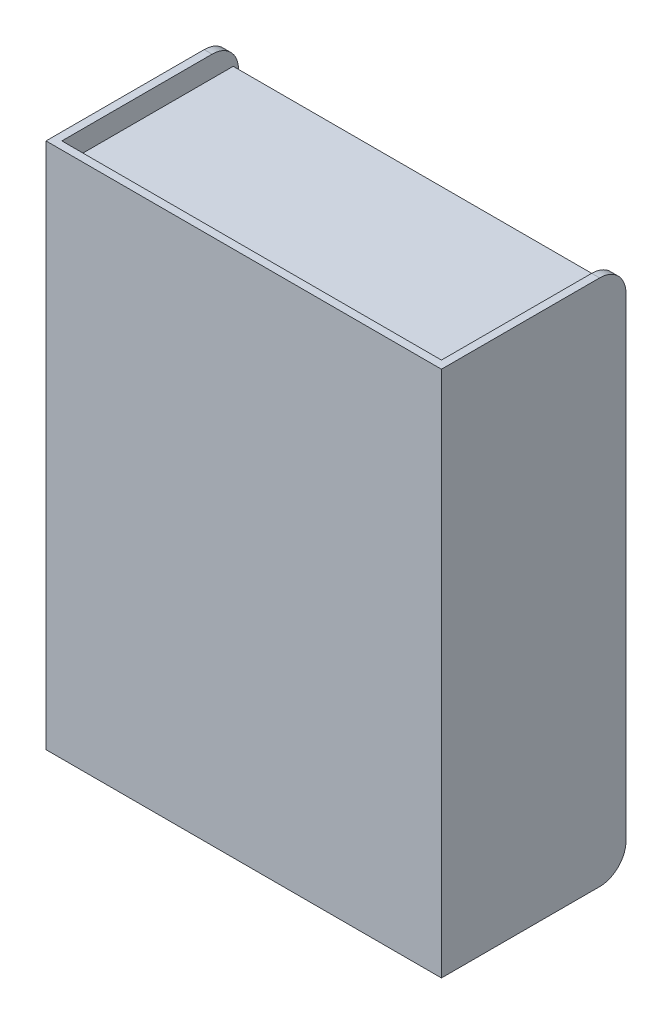
SolidWorks part; units mm, degrees
material "Oak"
ref_plane "Front Plane" through (0, 0, 0) normal (0, 0, 1) x (1, 0, 0)
ref_plane "Top Plane" through (0, 0, 0) normal (0, 1, 0) x (1, 0, 0)
ref_plane "Right Plane" through (0, 0, 0) normal (1, 0, 0) x (0, 0, -1)
sketch "Sketch1" plane through (0, 0, 0) normal (0, 0, 1) x (1, 0, 0)
  line L0 (94.3398, 450) -> (94.3398, 900) construction
  line L1 (-655.6602, 2000) -> (844.3398, 2000)
  line L2 (-655.6602, 2000) -> (-655.6602, 0)
  line L3 (-655.6602, 0) -> (844.3398, 0)
  line L4 (844.3398, 2000) -> (844.3398, 0)
  line L5 (-655.6602, 2000) -> (844.3398, 0) construction
  line L6 (-655.6602, 0) -> (844.3398, 2000) construction
  line L7 (-655.6602, 2000) -> (-625.6602, 2000)
  line L8 (-655.6602, 2000) -> (-655.6602, 0)
  line L9 (-655.6602, 0) -> (-625.6602, 0)
  line L10 (-625.6602, 2000) -> (-625.6602, 0)
  line L11 (844.3398, 0) -> (814.3398, 0)
  line L12 (814.3398, 2000) -> (814.3398, 0)
  line L13 (844.3398, 2000) -> (814.3398, 2000)
  line L14 (844.3398, 2000) -> (844.3398, 0)
  line L15 (-266.1102, 1000) -> (-1179.071, 1000) construction
  line L16 (-625.6602, 1920) -> (814.3398, 1920)
  line L17 (-625.6602, 1920) -> (-625.6602, 1890)
  line L18 (-625.6602, 1890) -> (814.3398, 1890)
  line L19 (814.3398, 1920) -> (814.3398, 1890)
  line L20 (-625.6602, 110) -> (814.3398, 110)
  line L21 (814.3398, 80) -> (814.3398, 110)
  line L22 (-625.6602, 80) -> (814.3398, 80)
  line L23 (-625.6602, 80) -> (-625.6602, 110)
  line L25 (-625.6602, 1015) -> (814.3398, 1015)
  line L26 (-625.6602, 1015) -> (-625.6602, 985)
  line L27 (-625.6602, 985) -> (814.3398, 985)
  line L28 (814.3398, 1015) -> (814.3398, 985)
  line L29 (-625.6602, 1015) -> (814.3398, 985) construction
  line L30 (-625.6602, 985) -> (814.3398, 1015) construction
  point P0 (94.3398, 1000)
  point P26 (94.3398, 1000)
  dimension "D1" = 2000
  dimension "D2" = 1500
  dimension "D3" = 30
  dimension "D4" = 30
  dimension "D5" = 80
  dimension "D6" = 80
  dimension "D7" = 30
sketch "Sketch2" plane through (0, 0, 0) normal (0, 0, 1) x (1, 0, 0)
  line L1 (-655.6602, 2000) -> (-625.6602, 2000)
  line L2 (-655.6602, 2000) -> (-655.6602, 0)
  line L3 (-655.6602, 0) -> (-625.6602, 0)
  line L4 (-625.6602, 2000) -> (-625.6602, 0)
  line L5 (-655.6602, 2000) -> (-625.6602, 0) construction
  line L6 (-655.6602, 0) -> (-625.6602, 2000) construction
  line L7 (844.3398, 0) -> (814.3398, 0)
  line L8 (844.3398, 0) -> (844.3398, 2000)
  line L9 (844.3398, 2000) -> (814.3398, 2000)
  line L10 (814.3398, 0) -> (814.3398, 2000)
  line L11 (844.3398, 0) -> (814.3398, 2000) construction
  line L12 (844.3398, 2000) -> (814.3398, 0) construction
  point P4 (-640.6602, 1000)
  point P11 (829.3398, 1000)
extrude "Boss-Extrude1" add sketch "Sketch2" along normal blind 700
sketch "Sketch3" plane through (0, 0, 700) normal (0, 0, 1) x (1, 0, 0)
  line L1 (-625.6602, 2000) -> (814.3398, 2000)
  line L2 (-625.6602, 2000) -> (-625.6602, 0)
  line L3 (-625.6602, 0) -> (814.3398, 0)
  line L4 (814.3398, 2000) -> (814.3398, 0)
  line L5 (-625.6602, 2000) -> (814.3398, 0) construction
  line L6 (-625.6602, 0) -> (814.3398, 2000) construction
  point P4 (94.3398, 1000)
extrude "Boss-Extrude2" add sketch "Sketch3" against normal blind 30 separate body
sketch "Sketch4" plane through (0, 0, 670) normal (0, 0, -1) x (-1, 0, 0)
  line L1 (-814.3398, 1920) -> (625.6602, 1920)
  line L2 (-814.3398, 1920) -> (-814.3398, 1890)
  line L3 (-814.3398, 1890) -> (625.6602, 1890)
  line L4 (625.6602, 1920) -> (625.6602, 1890)
  line L5 (-814.3398, 1920) -> (625.6602, 1890) construction
  line L6 (-814.3398, 1890) -> (625.6602, 1920) construction
  line L7 (-814.3398, 110) -> (625.6602, 110)
  line L8 (-814.3398, 110) -> (-814.3398, 80)
  line L9 (-814.3398, 80) -> (625.6602, 80)
  line L10 (625.6602, 110) -> (625.6602, 80)
  line L11 (-814.3398, 110) -> (625.6602, 80) construction
  line L12 (-814.3398, 80) -> (625.6602, 110) construction
  point P4 (-94.3398, 1905)
  point P11 (-94.3398, 95)
extrude "Boss-Extrude3" add sketch "Sketch4" along normal blind 650
sketch "Sketch5" plane through (0, 0, 670) normal (0, 0, -1) x (-1, 0, 0)
  line L1 (-814.3398, 1015) -> (625.6602, 1015)
  line L2 (-814.3398, 1015) -> (-814.3398, 985)
  line L3 (-814.3398, 985) -> (625.6602, 985)
  line L4 (625.6602, 1015) -> (625.6602, 985)
  line L5 (-814.3398, 1015) -> (625.6602, 985) construction
  line L6 (-814.3398, 985) -> (625.6602, 1015) construction
  point P4 (-94.3398, 1000)
extrude "Boss-Extrude4" add sketch "Sketch5" along normal blind 620
fillet "Fillet1" radius 100 4 edges at (829.3398, 0, 0) (-640.6602, 0, 0) (-640.6602, 2000, 0) (829.3398, 2000, 0)
sketch "Sketch7" plane through (0, 0, 20) normal (0, 0, -1) x (-1, 0, 0)
  line L0 (625.6602, 110) -> (-814.3398, 110) construction
  line L1 (-814.3398, 1890) -> (-94.3398, 1890)
  line L2 (-814.3398, 1890) -> (-814.3398, 110)
  line L3 (-814.3398, 110) -> (-94.3398, 110)
  line L4 (-94.3398, 1890) -> (-94.3398, 110)
  line L5 (-814.3398, 1890) -> (-94.3398, 110) construction
  line L6 (-814.3398, 110) -> (-94.3398, 1890) construction
  point P4 (-94.3398, 1727.5)
  point P5 (-454.3398, 1000)
  point P6 (-94.3398, 1452.5)
  dimension "D1" = 720
extrude "Boss-Extrude7" add sketch "Sketch7" against normal blind 20 separate body
sketch "Sketch8" plane through (0, 0, 20) normal (0, 0, -1) x (-1, 0, 0)
  line L0 (625.6602, 110) -> (-814.3398, 110) construction
  line L5 (625.6602, 1890) -> (-94.3398, 1890)
  line L6 (625.6602, 1890) -> (625.6602, 110)
  line L7 (625.6602, 110) -> (-94.3398, 110)
  line L8 (-94.3398, 1890) -> (-94.3398, 110)
  line L9 (625.6602, 1890) -> (-94.3398, 110) construction
  line L10 (625.6602, 110) -> (-94.3398, 1890) construction
  point P4 (-94.3398, 547.5)
  point P7 (265.6602, 1000)
extrude "Boss-Extrude8" add sketch "Sketch8" against normal blind 20 separate body
sketch "Sketch9" plane through (0, 0, 20) normal (0, 0, -1) x (-1, 0, 0)
  line L0 (625.6602, 1890) -> (625.6602, 1920) construction
  line L1 (625.6602, 1015) -> (-814.3398, 1015) construction
  circle A0 centre (-4.3398, 1015) radius 20
  dimension "D1" = 630
  dimension "D2" = 0
extrude "Boss-Extrude9" add sketch "Sketch9" along normal blind 25 separate body
sketch "Sketch10" plane through (0, 0, -5) normal (0, 0, -1) x (-1, 0, 0)
  circle A0 centre (-4.3398, 1015) radius 25
  dimension "D1" = 50
extrude "Boss-Extrude10" add sketch "Sketch10" along normal blind 20
fillet "Fillet2" radius 15 1 edges at (-20.6602, 1015, -25)
pattern_linear "LPattern7" count 2 spacing 180 along (1, 0, 0) of "Boss-Extrude9", "Boss-Extrude10"
sketch "Sketch15" plane through (0, 0, -5) normal (0, 0, -1) x (-1, 0, 0)
  circle A0 centre (-184.3398, 1015) radius 25
  dimension "D1" = 50
extrude "Boss-Extrude14" add sketch "Sketch15" along normal blind 20
fillet "Fillet5" radius 15 1 edges at (159.3398, 1015, -25)
